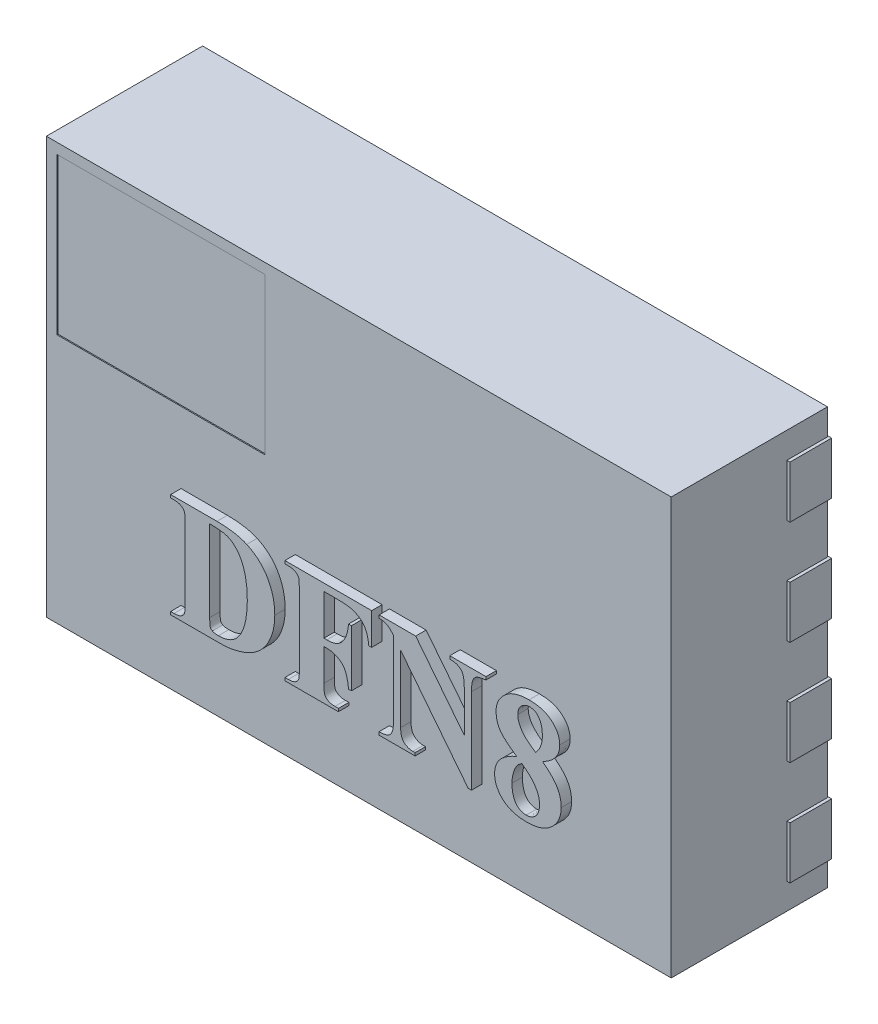
SolidWorks part; units mm, degrees
ref_plane "Front Plane" through (0, 0, 0) normal (0, 0, 1) x (1, 0, 0)
ref_plane "Top Plane" through (0, 0, 0) normal (0, 1, 0) x (1, 0, 0)
ref_plane "Right Plane" through (0, 0, 0) normal (1, 0, 0) x (0, 0, -1)
sketch "Sketch1" plane through (0, 0, 0) normal (0, 0, 1) x (1, 0, 0)
  line L1 (-1.5, -1) -> (1.5, -1) construction
  line L2 (-1.5, -1) -> (-1.5, 1) construction
  line L3 (-1.5, 1) -> (1.5, 1) construction
  line L4 (1.5, -1) -> (1.5, 1) construction
  line L5 (-1.5, -1) -> (1.5, 1) construction
  line L6 (-1.5, 1) -> (1.5, -1) construction
  line L7 (-1.505, 0.875) -> (-1.155, 0.875)
  line L8 (-1.505, 0.875) -> (-1.505, 0.625)
  line L9 (-1.505, 0.625) -> (-1.155, 0.625)
  line L10 (-1.155, 0.875) -> (-1.155, 0.625)
  point P0 (0, 0)
  point P10 (-1.505, 0.75)
  point P11 (-1.5, 0)
  dimension "D1" = 3
  dimension "D2" = 2
  dimension "D3" = 0.25
  dimension "D4" = 0.35
  dimension "D5" = 0.005
  dimension "D6" = 0.75
extrude "Pin1" add sketch "Sketch1" along normal blind 0.2
pattern_linear "LPattern1" count 4 spacing 0.5 along (0, -1, 0) count 2 spacing 2.67 along (1, 0, 0) of "Pin1"
sketch "Sketch5" plane through (0, 0, 0) normal (0, 0, 1) x (1, 0, 0)
  line L0 (-0.8, 0.625) -> (-0.8, -0.875)
  line L1 (-0.8, -0.875) -> (0.8, -0.875)
  line L2 (0.8, -0.875) -> (0.8, 0.875)
  line L4 (0.8, 0.875) -> (-0.55, 0.875)
  line L5 (0, -0.875) -> (0, 0) construction
  line L6 (-0.8, 0) -> (0, 0) construction
  line L7 (-0.55, 0.875) -> (-0.8, 0.625)
  point P0 (0.8, 0.8509)
  dimension "D1" = 1.75
  dimension "D2" = 1.6
  dimension "D5" = 135
  dimension "D6" = 0.25
  dimension "D7" = 0.875
extrude "GND Pad" add sketch "Sketch5" along normal blind 0.2 separate body
sketch "Sketch2" plane through (0, 0, 0) normal (0, 0, 1) x (1, 0, 0)
  line L1 (-1.5, -1) -> (1.5, -1)
  line L2 (-1.5, -1) -> (-1.5, 1)
  line L3 (-1.5, 1) -> (1.5, 1)
  line L4 (1.5, -1) -> (1.5, 1)
  line L5 (-1.5, -1) -> (1.5, 1) construction
  line L6 (-1.5, 1) -> (1.5, -1) construction
  point P0 (0, 0)
  dimension "D1" = 3
  dimension "D2" = 2
extrude "Body" add sketch "Sketch2" along normal blind 0.75 from offset 0.005 separate body
sketch "Sketch3" plane through (0, 0, 0.755) normal (0, 0, 1) x (1, 0, 0)
  line L2 (1.5, 1) -> (-1.5, 1) construction
  line L3 (-1.45, 0.95) -> (-0.45, 0.95)
  line L4 (-1.45, 0.95) -> (-1.45, 0.2)
  line L5 (-1.45, 0.2) -> (-0.45, 0.2)
  line L6 (-0.45, 0.95) -> (-0.45, 0.2)
  line L7 (-1.5, 1) -> (-1.5, -1) construction
  dimension "D1" = 0.05
  dimension "D2" = 0.05
  dimension "D3" = 1
  dimension "D4" = 0.75
extrude "Pin1Silk" cut sketch "Sketch3" against normal blind 0.005
sketch "Sketch4" plane through (0, 0, 0.755) normal (0, 0, 1) x (1, 0, 0)
  text T0 "<b>DFN8</b>" font "Times New Roman" height 0.5
extrude "Text" add sketch "Sketch4" along normal blind 0.05
